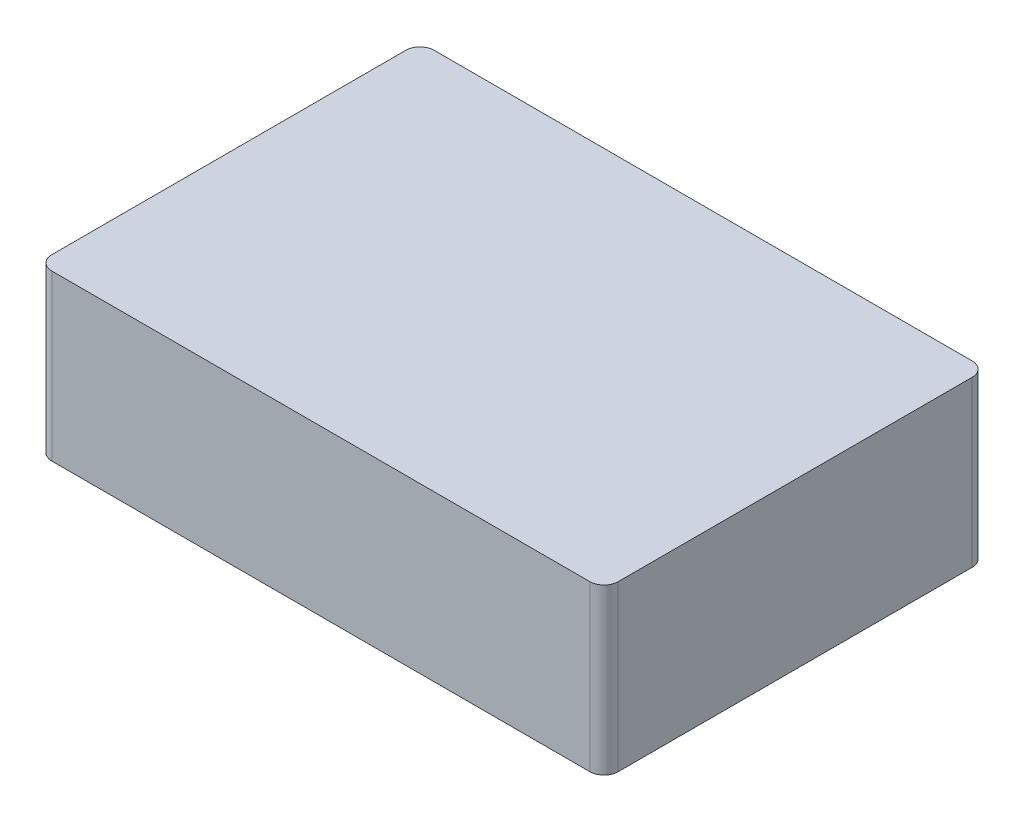
SolidWorks part; units mm, degrees
ref_plane "Front Plane" through (0, 0, 0) normal (0, 0, 1) x (1, 0, 0)
ref_plane "Top Plane" through (0, 0, 0) normal (0, 1, 0) x (1, 0, 0)
ref_plane "Right Plane" through (0, 0, 0) normal (1, 0, 0) x (0, 0, -1)
sketch "Sketch1" plane through (0, 0, 0) normal (0, 1, 0) x (1, 0, 0)
  line L1 (0, 0) -> (80, 0)
  line L2 (0, 0) -> (0, 54)
  line L3 (0, 54) -> (80, 54)
  line L4 (80, 0) -> (80, 54)
  dimension "D1" = 80
  dimension "D2" = 54
extrude "Boss-Extrude2" add sketch "Sketch1" along normal blind 23.25
fillet "Fillet1" radius 2 4 edges at (0, 11.625, -54) (0, 11.625, 0) (80, 11.625, -54) (80, 11.625, 0)
